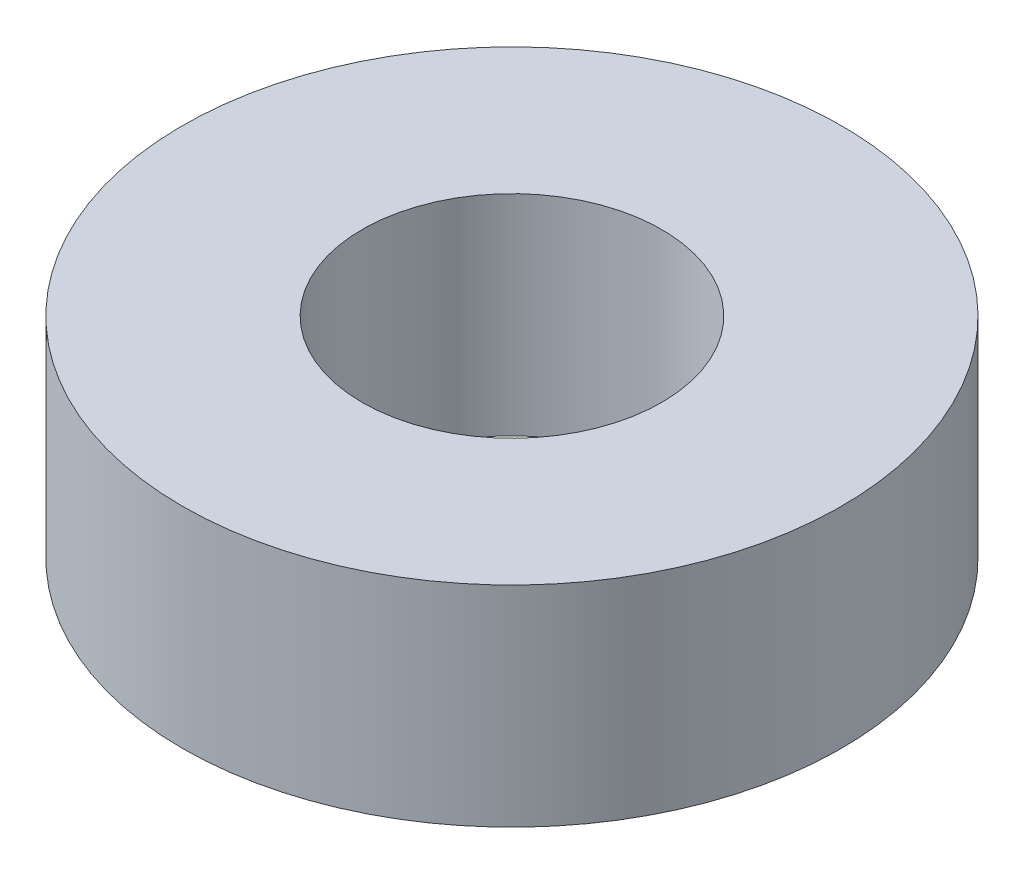
SolidWorks part; units mm, degrees
ref_plane "Front Plane" through (0, 0, 0) normal (0, 0, 1) x (1, 0, 0)
ref_plane "Top Plane" through (0, 0, 0) normal (0, 1, 0) x (1, 0, 0)
ref_plane "Right Plane" through (0, 0, 0) normal (1, 0, 0) x (0, 0, -1)
sketch "Sketch2" plane through (0, 0, 0) normal (0, 1, 0) x (1, 0, 0)
  circle A0 centre (0, 0) radius 11
  circle A1 centre (0, 0) radius 5
  dimension "D1" = 22
  dimension "D2" = 10
extrude "Boss-Extrude1" add sketch "Sketch2" along normal blind 7
